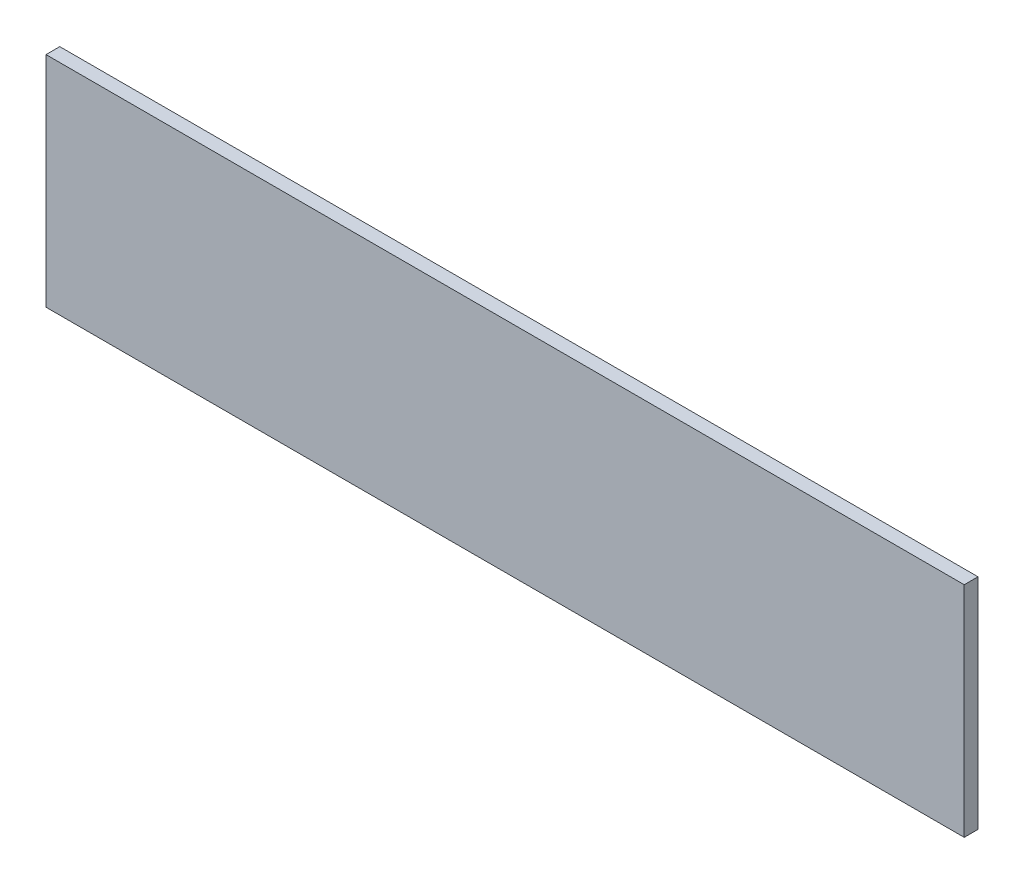
SolidWorks part; units mm, degrees
ref_plane "Plan de face" through (0, 0, 0) normal (0, 0, 1) x (1, 0, 0)
ref_plane "Plan de dessus" through (0, 0, 0) normal (0, 1, 0) x (1, 0, 0)
ref_plane "Plan de droite" through (0, 0, 0) normal (1, 0, 0) x (0, 0, -1)
sketch "Esquisse1" plane through (0, 0, 0) normal (0, 0, 1) x (1, 0, 0)
  line L1 (-58.9086, 34.3841) -> (141.0914, 34.3841)
  line L2 (-58.9086, 34.3841) -> (-58.9086, -13.2739)
  line L3 (-58.9086, -13.2739) -> (141.0914, -13.2739)
  line L4 (141.0914, 34.3841) -> (141.0914, -13.2739)
extrude "Boss.-Extru.1" add sketch "Esquisse1" along normal blind 3
